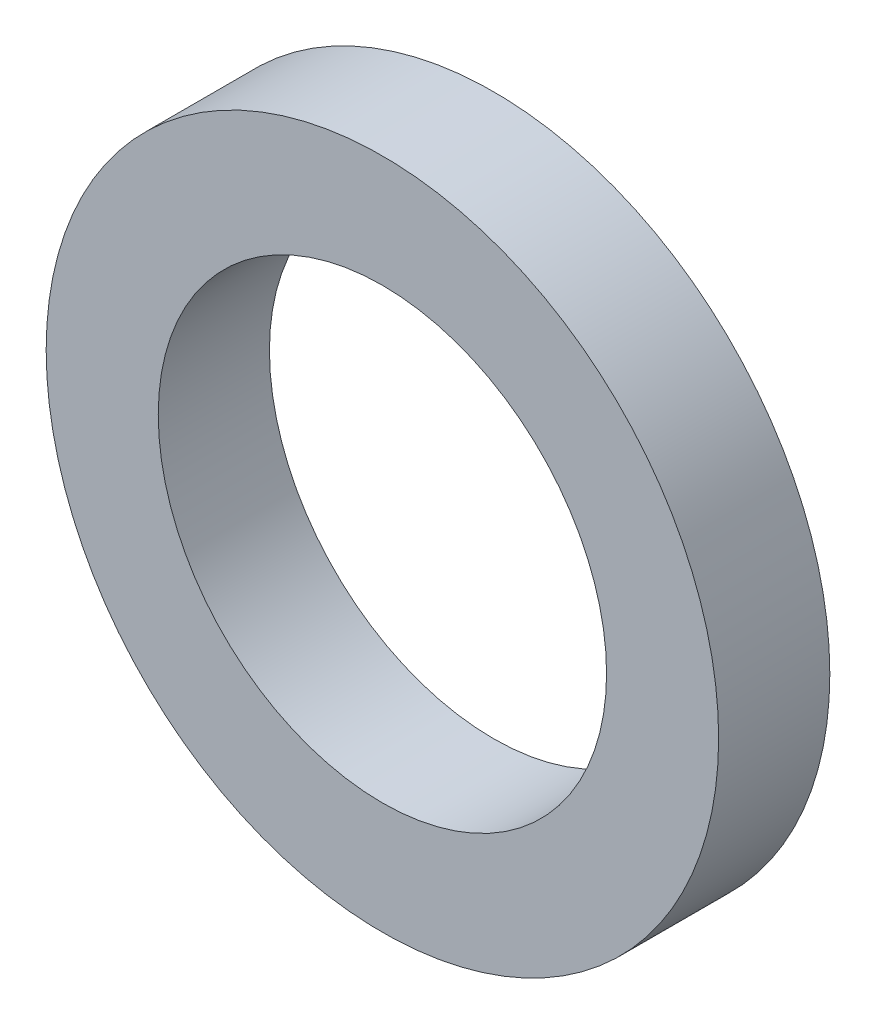
SolidWorks part; units mm, degrees
ref_plane "Front Plane" through (0, 0, 0) normal (0, 0, 1) x (1, 0, 0)
ref_plane "Top Plane" through (0, 0, 0) normal (0, 1, 0) x (1, 0, 0)
ref_plane "Right Plane" through (0, 0, 0) normal (1, 0, 0) x (0, 0, -1)
sketch "Sketch1" plane through (0, 0, 0) normal (0, 1, 0) x (1, 0, 0)
  line L0 (1.5875, -0.7874) -> (2.3812, -0.7874)
  line L1 (2.3812, -0.7874) -> (2.3812, 0)
  line L2 (2.3812, 0) -> (1.5875, 0)
  line L3 (1.5875, 0) -> (1.5875, -0.7874)
  line L4 (0, 0) -> (0, -0.7874) construction
revolve "Revolve1" add sketch "Sketch1" angle 360 about L4
